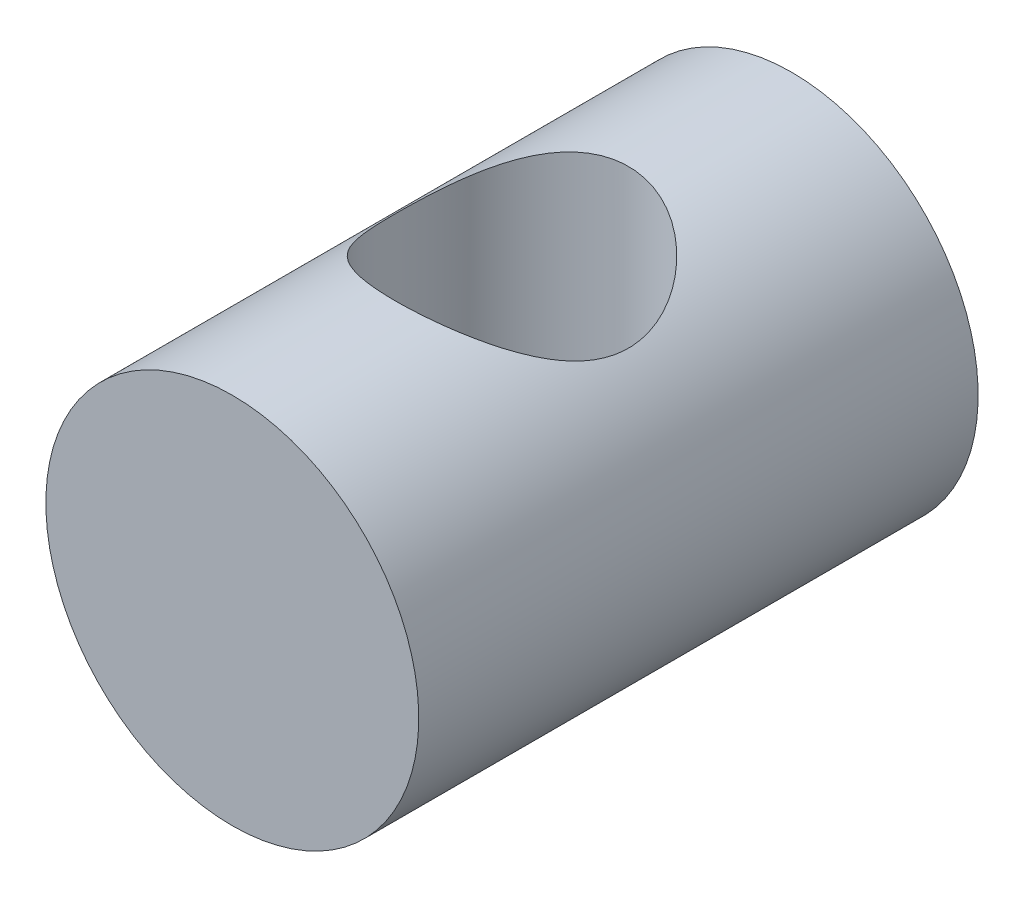
SolidWorks part; units mm, degrees
material "Aleación 1060"
ref_plane "Alzado" through (0, 0, 0) normal (0, 0, 1) x (1, 0, 0)
ref_plane "Planta" through (0, 0, 0) normal (0, 1, 0) x (1, 0, 0)
ref_plane "Vista lateral" through (0, 0, 0) normal (1, 0, 0) x (0, 0, -1)
sketch "Croquis2" plane through (0, 0, 0) normal (1, 0, 0) x (0, 0, -1)
  line L1 (-6, 4) -> (6, 4)
  line L2 (-6, 4) -> (-6, 0)
  line L3 (-6, 0) -> (6, 0)
  line L4 (6, 4) -> (6, 0)
  dimension "D1" = 4
  dimension "D2" = 12
revolve "Revolución5" add sketch "Croquis2" angle 360 about L3
sketch "Croquis3" plane through (0, 0, 0) normal (0, 1, 0) x (1, 0, 0)
  circle A0 centre (0, 0) radius 2.5
  dimension "D1" = 5
extrude "Cortar-Extruir1" cut sketch "Croquis3" against normal through all and the other way through all
